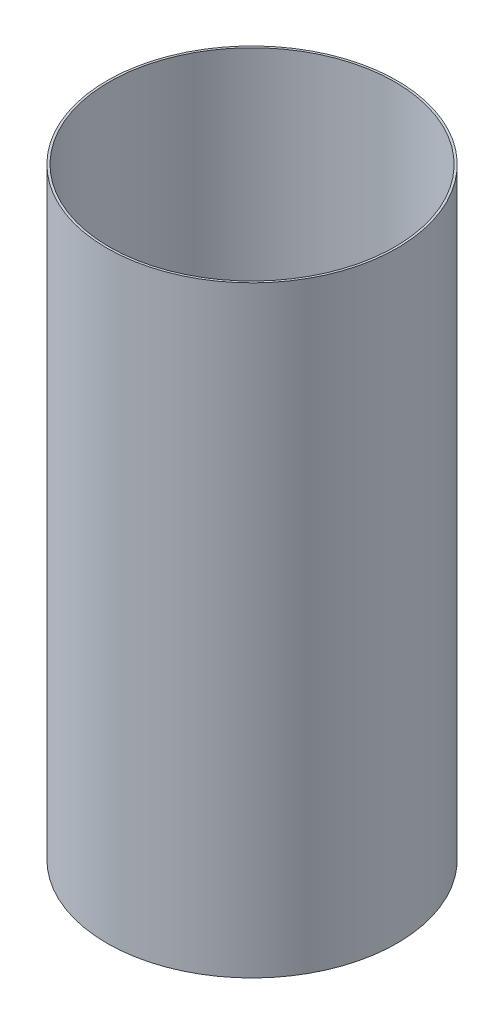
SolidWorks part; units mm, degrees
ref_plane "Alzado" through (0, 0, 0) normal (0, 0, 1) x (1, 0, 0)
ref_plane "Planta" through (0, 0, 0) normal (0, 1, 0) x (1, 0, 0)
ref_plane "Vista lateral" through (0, 0, 0) normal (1, 0, 0) x (0, 0, -1)
sketch "Croquis1" plane through (0, 0, 0) normal (0, 1, 0) x (1, 0, 0)
  circle A0 centre (0, 0) radius 35.605
  circle A1 centre (0, 0) radius 36.15
  dimension "D1" = 71.21
  dimension "D2" = 72.3
extrude "Saliente-Extruir1" add sketch "Croquis1" along normal blind 150
